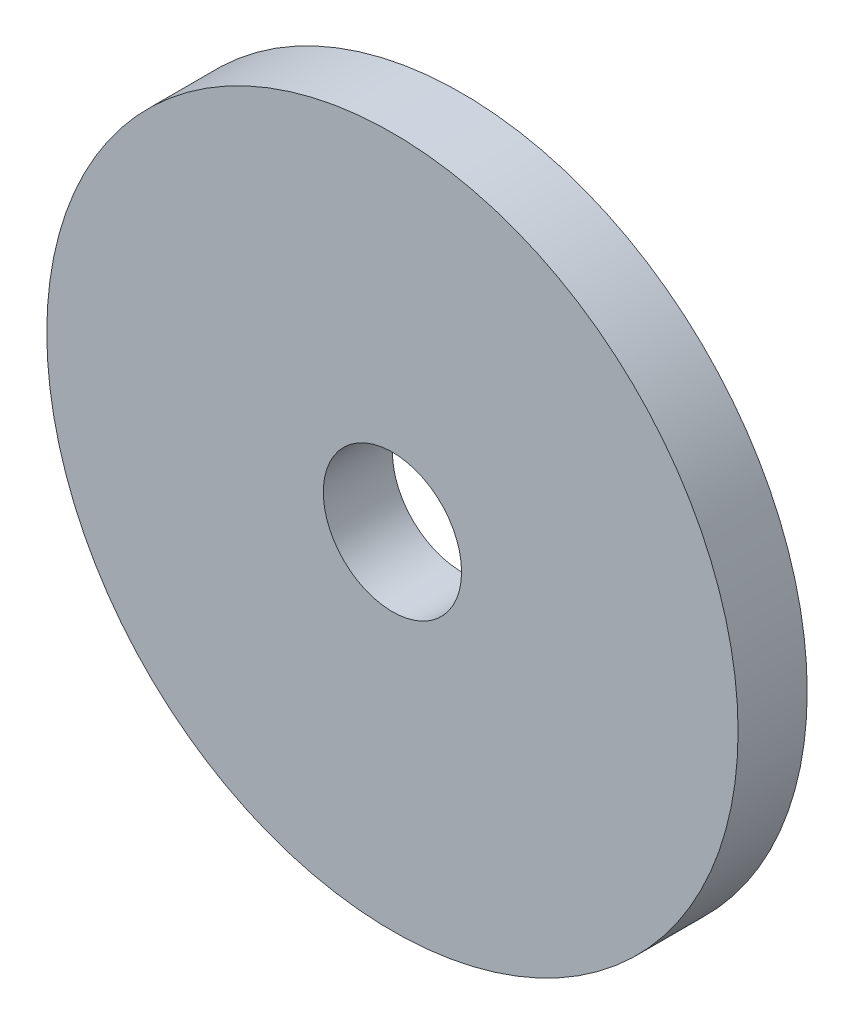
SolidWorks part; units mm, degrees
ref_plane "Front Plane" through (0, 0, 0) normal (0, 0, 1) x (1, 0, 0)
ref_plane "Top Plane" through (0, 0, 0) normal (0, 1, 0) x (1, 0, 0)
ref_plane "Right Plane" through (0, 0, 0) normal (1, 0, 0) x (0, 0, -1)
sketch "Sketch1" plane through (0, 0, 0) normal (0, 0, 1) x (1, 0, 0)
  circle A0 centre (0, 0) radius 50
  circle A1 centre (0, 0) radius 10
  dimension "D1" = 100
  dimension "D2" = 20
extrude "Boss-Extrude1" add sketch "Sketch1" along normal blind 10
